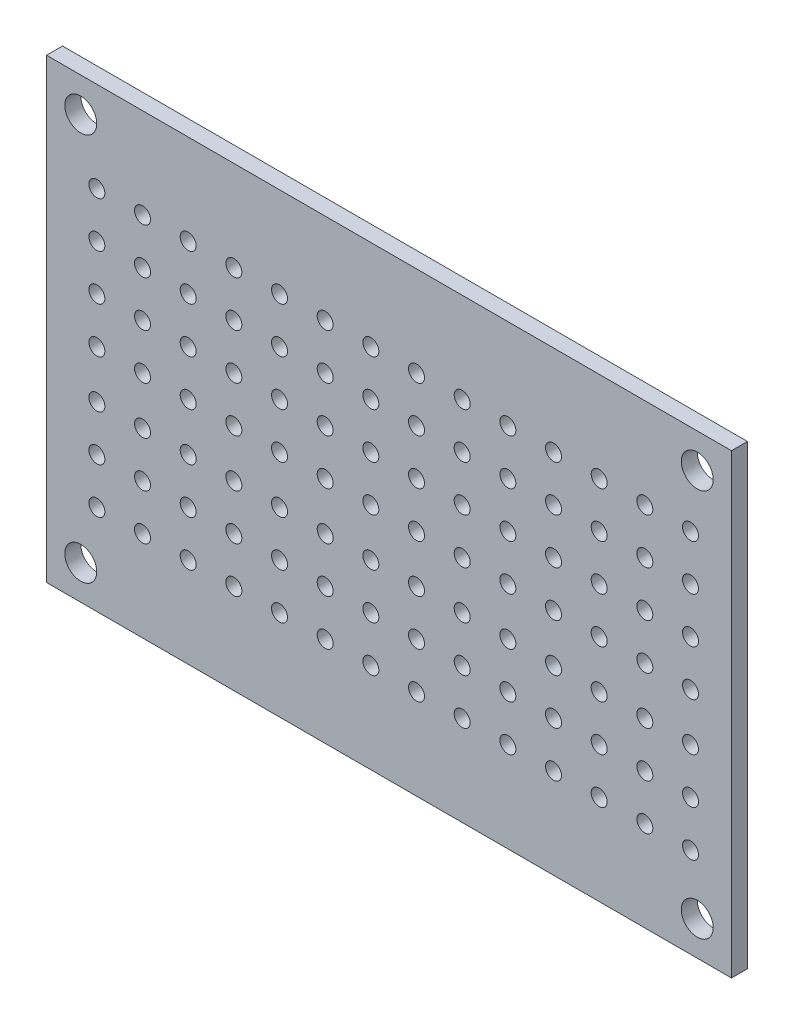
SolidWorks part; units mm, degrees
ref_plane "Front Plane" through (0, 0, 0) normal (0, 0, 1) x (1, 0, 0)
ref_plane "Top Plane" through (0, 0, 0) normal (0, 1, 0) x (1, 0, 0)
ref_plane "Right Plane" through (0, 0, 0) normal (1, 0, 0) x (0, 0, -1)
sketch "Sketch1" plane through (0, 0, 0) normal (0, 0, 1) x (1, 0, 0)
  line L0 (-24.2685, 0) -> (41.9703, 0) construction
  line L1 (38.1, -25.4) -> (-38.1, -25.4)
  line L2 (38.1, -25.4) -> (38.1, 25.4)
  line L3 (38.1, 25.4) -> (-38.1, 25.4)
  line L4 (-38.1, -25.4) -> (-38.1, 25.4)
  line L6 (0, 20.771) -> (0, -20.9138) construction
  circle A0 centre (-34.29, 21.59) radius 1.778
  circle A1 centre (-34.29, -21.59) radius 1.778
  circle A2 centre (34.29, 21.59) radius 1.778
  circle A3 centre (34.29, -21.59) radius 1.778
  point P0 (0, 0)
  dimension "D3" = 3.556
  dimension "D1" = 3.81
  dimension "D2" = 3.81
  dimension "D4" = 76.2
  dimension "D5" = 50.8
  dimension "D6" = 38.1
  dimension "D7" = 25.4
extrude "Boss-Extrude1" add sketch "Sketch1" along normal blind 1.778
sketch "Sketch2" plane through (0, 0, 0) normal (0, 0, -1) x (-1, 0, 0)
  line L0 (27.4203, 15.354) -> (17.2603, 15.354) construction
  line L1 (42.0084, 0) -> (-56.0497, 0) construction
  line L2 (27.4203, -15.354) -> (17.2603, -15.354) construction
  circle A0 centre (27.4203, 15.354) radius 0.889
  circle A1 centre (32.5003, 15.354) radius 0.889
  circle A2 centre (27.4203, 10.274) radius 0.889
  circle A3 centre (32.5003, 10.274) radius 0.889
  circle A4 centre (17.2603, 15.354) radius 0.889
  circle A5 centre (22.3403, 15.354) radius 0.889
  circle A6 centre (17.2603, 10.274) radius 0.889
  circle A7 centre (22.3403, 10.274) radius 0.889
  circle A8 centre (17.2603, 5.194) radius 0.889
  circle A9 centre (22.3403, 5.194) radius 0.889
  circle A10 centre (17.2603, 0.114) radius 0.889
  circle A11 centre (22.3403, 0.114) radius 0.889
  circle A12 centre (7.1003, 15.354) radius 0.889
  circle A13 centre (12.1803, 15.354) radius 0.889
  circle A14 centre (7.1003, 10.274) radius 0.889
  circle A15 centre (12.1803, 10.274) radius 0.889
  circle A16 centre (7.1003, 5.194) radius 0.889
  circle A17 centre (12.1803, 5.194) radius 0.889
  circle A18 centre (7.1003, 0.114) radius 0.889
  circle A19 centre (12.1803, 0.114) radius 0.889
  circle A20 centre (-3.0597, 15.354) radius 0.889
  circle A21 centre (2.0203, 15.354) radius 0.889
  circle A22 centre (27.4203, 5.194) radius 0.889
  circle A23 centre (32.5003, 5.194) radius 0.889
  circle A24 centre (27.4203, 0.114) radius 0.889
  circle A25 centre (32.5003, 0.114) radius 0.889
  circle A26 centre (-3.0597, 10.274) radius 0.889
  circle A27 centre (2.0203, 10.274) radius 0.889
  circle A28 centre (-3.0597, 5.194) radius 0.889
  circle A29 centre (2.0203, 5.194) radius 0.889
  circle A30 centre (-3.0597, 0.114) radius 0.889
  circle A31 centre (2.0203, 0.114) radius 0.889
  circle A32 centre (-13.2197, 15.354) radius 0.889
  circle A33 centre (-8.1397, 15.354) radius 0.889
  circle A34 centre (-13.2197, 10.274) radius 0.889
  circle A35 centre (-8.1397, 10.274) radius 0.889
  circle A36 centre (-13.2197, 5.194) radius 0.889
  circle A37 centre (-8.1397, 5.194) radius 0.889
  circle A38 centre (-13.2197, 0.114) radius 0.889
  circle A39 centre (-8.1397, 0.114) radius 0.889
  circle A40 centre (-23.3797, 15.354) radius 0.889
  circle A41 centre (-18.2997, 15.354) radius 0.889
  circle A42 centre (-23.3797, 10.274) radius 0.889
  circle A43 centre (-18.2997, 10.274) radius 0.889
  circle A44 centre (-23.3797, 5.194) radius 0.889
  circle A45 centre (-18.2997, 5.194) radius 0.889
  circle A46 centre (-23.3797, 0.114) radius 0.889
  circle A47 centre (-18.2997, 0.114) radius 0.889
  circle A48 centre (-33.5397, 15.354) radius 0.889
  circle A49 centre (-28.4597, 15.354) radius 0.889
  circle A50 centre (-33.5397, 10.274) radius 0.889
  circle A51 centre (-28.4597, 10.274) radius 0.889
  circle A52 centre (-33.5397, 5.194) radius 0.889
  circle A53 centre (-28.4597, 5.194) radius 0.889
  circle A54 centre (-33.5397, 0.114) radius 0.889
  circle A55 centre (-28.4597, 0.114) radius 0.889
  circle A56 centre (-28.4597, -5.194) radius 0.889
  circle A57 centre (-33.5397, -5.194) radius 0.889
  circle A58 centre (-28.4597, -10.274) radius 0.889
  circle A59 centre (-33.5397, -10.274) radius 0.889
  circle A60 centre (-28.4597, -15.354) radius 0.889
  circle A61 centre (-33.5397, -15.354) radius 0.889
  circle A62 centre (-18.2997, -5.194) radius 0.889
  circle A63 centre (-23.3797, -5.194) radius 0.889
  circle A64 centre (-18.2997, -10.274) radius 0.889
  circle A65 centre (-23.3797, -10.274) radius 0.889
  circle A66 centre (-18.2997, -15.354) radius 0.889
  circle A67 centre (-23.3797, -15.354) radius 0.889
  circle A68 centre (-8.1397, -5.194) radius 0.889
  circle A69 centre (-13.2197, -5.194) radius 0.889
  circle A70 centre (-8.1397, -10.274) radius 0.889
  circle A71 centre (-13.2197, -10.274) radius 0.889
  circle A72 centre (-8.1397, -15.354) radius 0.889
  circle A73 centre (-13.2197, -15.354) radius 0.889
  circle A74 centre (2.0203, -5.194) radius 0.889
  circle A75 centre (-3.0597, -5.194) radius 0.889
  circle A76 centre (2.0203, -10.274) radius 0.889
  circle A77 centre (-3.0597, -10.274) radius 0.889
  circle A78 centre (32.5003, -5.194) radius 0.889
  circle A79 centre (27.4203, -5.194) radius 0.889
  circle A80 centre (2.0203, -15.354) radius 0.889
  circle A81 centre (-3.0597, -15.354) radius 0.889
  circle A82 centre (12.1803, -5.194) radius 0.889
  circle A83 centre (7.1003, -5.194) radius 0.889
  circle A84 centre (12.1803, -10.274) radius 0.889
  circle A85 centre (7.1003, -10.274) radius 0.889
  circle A86 centre (12.1803, -15.354) radius 0.889
  circle A87 centre (7.1003, -15.354) radius 0.889
  circle A88 centre (22.3403, -5.194) radius 0.889
  circle A89 centre (17.2603, -5.194) radius 0.889
  circle A90 centre (22.3403, -10.274) radius 0.889
  circle A91 centre (17.2603, -10.274) radius 0.889
  circle A92 centre (22.3403, -15.354) radius 0.889
  circle A93 centre (17.2603, -15.354) radius 0.889
  circle A94 centre (32.5003, -10.274) radius 0.889
  circle A95 centre (27.4203, -10.274) radius 0.889
  circle A96 centre (32.5003, -15.354) radius 0.889
  circle A97 centre (27.4203, -15.354) radius 0.889
  dimension "D2" = 10.16
  dimension "D3" = 2
  dimension "D7" = 5.08
  dimension "D8" = 5.08
  dimension "D10" = 5.08
  dimension "D11" = 5.08
  dimension "D12" = 5.08
extrude "Cut-Extrude1" cut sketch "Sketch2" against normal through all
